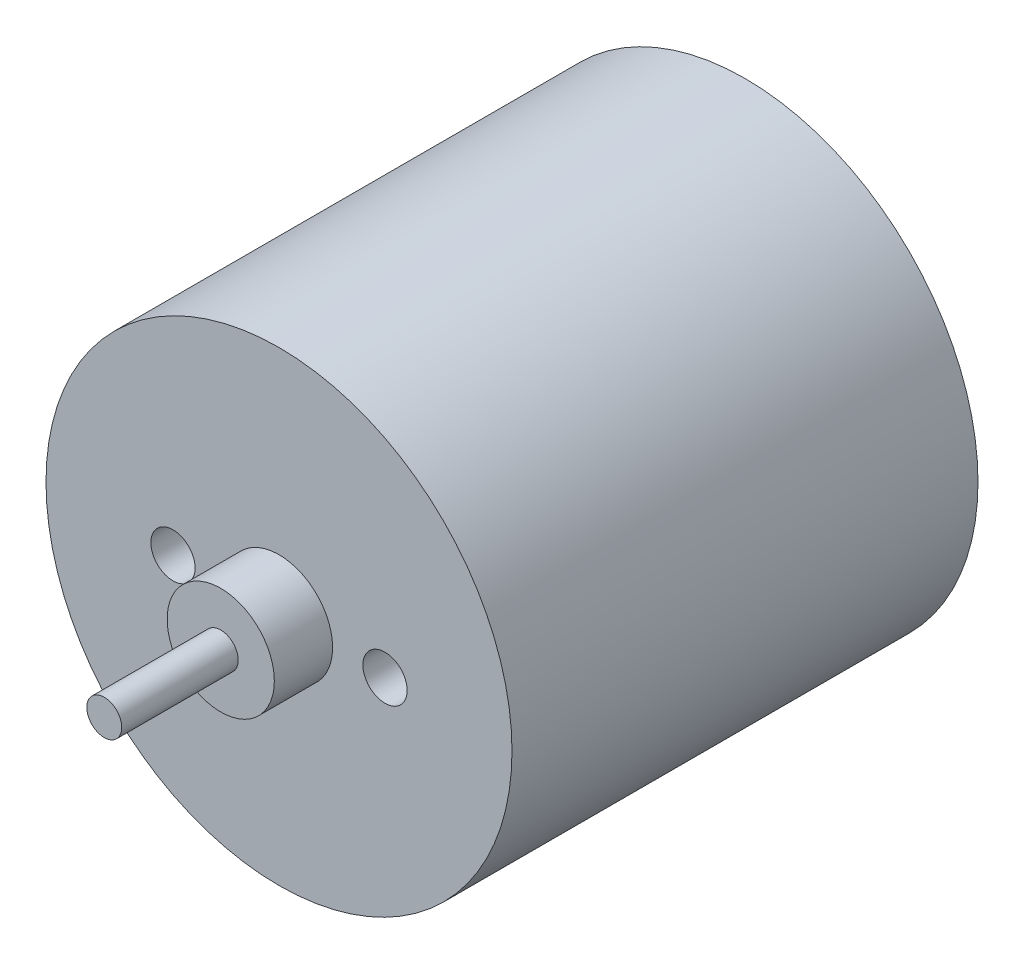
SolidWorks part; units mm, degrees
ref_plane "Front Plane" through (0, 0, 0) normal (0, 0, 1) x (1, 0, 0)
ref_plane "Top Plane" through (0, 0, 0) normal (0, 1, 0) x (1, 0, 0)
ref_plane "Right Plane" through (0, 0, 0) normal (1, 0, 0) x (0, 0, -1)
sketch "Sketch1" plane through (0, 0, 0) normal (0, 0, 1) x (1, 0, 0)
  circle A0 centre (0, 0) radius 12.7
  dimension "D1" = 25.4
extrude "Boss-Extrude1" add sketch "Sketch1" along normal blind 25.4
sketch "Sketch2" plane through (0, 0, 25.4) normal (0, 0, 1) x (1, 0, 0)
  circle A0 centre (0, 0) radius 2.921
  dimension "D1" = 5.842
extrude "Boss-Extrude2" add sketch "Sketch2" along normal blind 3.175
sketch "Sketch4" plane through (0, 0, 25.4) normal (0, 0, 1) x (1, 0, 0)
  circle A0 centre (-5.7785, 0) radius 1.2065
  circle A1 centre (5.7785, 0) radius 1.2065
  dimension "D1" = 2.413
  dimension "D2" = 5.7785
  dimension "D3" = 5.7785
extrude "Cut-Extrude1" cut sketch "Sketch4" against normal blind 7.62 contours A1 | A0
sketch "Sketch6" plane through (0, 0, 28.575) normal (0, 0, 1) x (1, 0, 0)
  circle A0 centre (0, 0) radius 0.9525
  dimension "D1" = 1.905
extrude "Boss-Extrude3" add sketch "Sketch6" along normal blind 6.35
